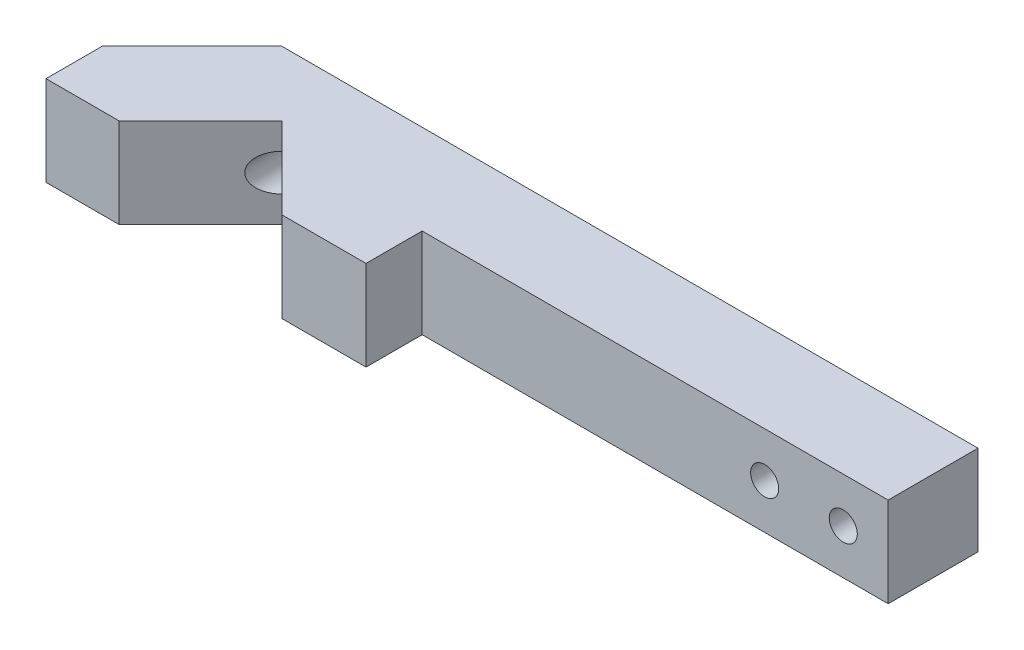
SolidWorks part; units mm, degrees
ref_plane "Front Plane" through (0, 0, 0) normal (0, 0, 1) x (1, 0, 0)
ref_plane "Top Plane" through (0, 0, 0) normal (0, 1, 0) x (1, 0, 0)
ref_plane "Right Plane" through (0, 0, 0) normal (1, 0, 0) x (0, 0, -1)
sketch "Sketch1" plane through (0, 0, 0) normal (0, 1, 0) x (1, 0, 0)
  line L0 (-35, -4) -> (-27, 4)
  line L1 (-27, 4) -> (35, 4)
  line L4 (35, 4) -> (35, -4)
  line L5 (-35, 4) -> (35, -4) construction
  line L6 (-35, -4) -> (35, 4) construction
  line L8 (-35, -4) -> (-35, -9)
  line L9 (-35, -9) -> (-28.5, -9)
  line L10 (-6.5, -4) -> (-6.5, -9)
  line L11 (-28.5, -9) -> (-21.25, -1.75)
  line L13 (-6.5, -4) -> (35, -4)
  line L14 (-14, -9) -> (-6.5, -9)
  line L16 (-21.25, -1.75) -> (-14, -9)
  point P0 (0, 0)
  dimension "D1" = 8
  dimension "D2" = 70
  dimension "D3" = 5
  dimension "D4" = 7.5
  dimension "D5" = 6.5
  dimension "D6" = 45
  dimension "D7" = 14.5
extrude "Boss-Extrude2" add sketch "Sketch1" along normal blind 8
hole_wizard "M4 Tapped Hole1" positions "Sketch3" profile "Sketch4" tap size "M4" standard "DIN"
sketch "Sketch3" plane through (0, 0, -4) normal (0, 0, -1) x (-1, 0, 0)
  line L0 (35, 8) -> (35, 0) construction
  point P0 (21.25, 4)
  dimension "D1" = 13.75
sketch "Sketch4" plane through (-21.25, 4, -4) normal (1, 0, 0) x (0, 1, 0)
  line L0 (0, 0) -> (0, 12.4914)
  line L1 (0, 12.4914) -> (1.65, 11.5)
  line L2 (1.65, 11.5) -> (1.65, 0)
  line L5 (1.65, 0) -> (0, 0)
  line L10 (0, 12.4914) -> (-1.65, 11.5) construction
  line L11 (0, -6.35) -> (0, 107.95) construction
  dimension "Tap Drill Dia." = 3.3
  dimension "Tap Drill Depth" = 11.5
  dimension "Drill Angle" = 118
cosmetic thread "Hole Thread1" parameters "D1"=8, "D2"=4
hole_wizard "M3 Tapped Hole1" positions "Sketch7" profile "Sketch8" tap size "M3" standard "DIN"
sketch "Sketch7" plane through (0, 0, -4) normal (0, 0, -1) x (-1, 0, 0)
  line L0 (-35, 8) -> (-35, 0) construction
  point P0 (-31, 4)
  point P2 (-24, 4)
  point P11 (-31, 4)
  point P12 (0, 0)
  dimension "D1" = 4
  dimension "D2" = 7
sketch "Sketch8" plane through (31, 4, -4) normal (1, 0, 0) x (0, 1, 0)
  line L0 (0, 0) -> (0, 9.2511)
  line L1 (0, 9.2511) -> (1.25, 8.5)
  line L2 (1.25, 8.5) -> (1.25, 0)
  line L5 (1.25, 0) -> (0, 0)
  line L10 (0, 9.2511) -> (-1.25, 8.5) construction
  line L11 (0, -6.35) -> (0, 107.95) construction
  dimension "Tap Drill Dia." = 2.5
  dimension "Tap Drill Depth" = 8.5
  dimension "Drill Angle" = 118
cosmetic thread "Hole Thread4" parameters "D1"=6, "D2"=3
cosmetic thread "Hole Thread5" parameters "D1"=6, "D2"=3
